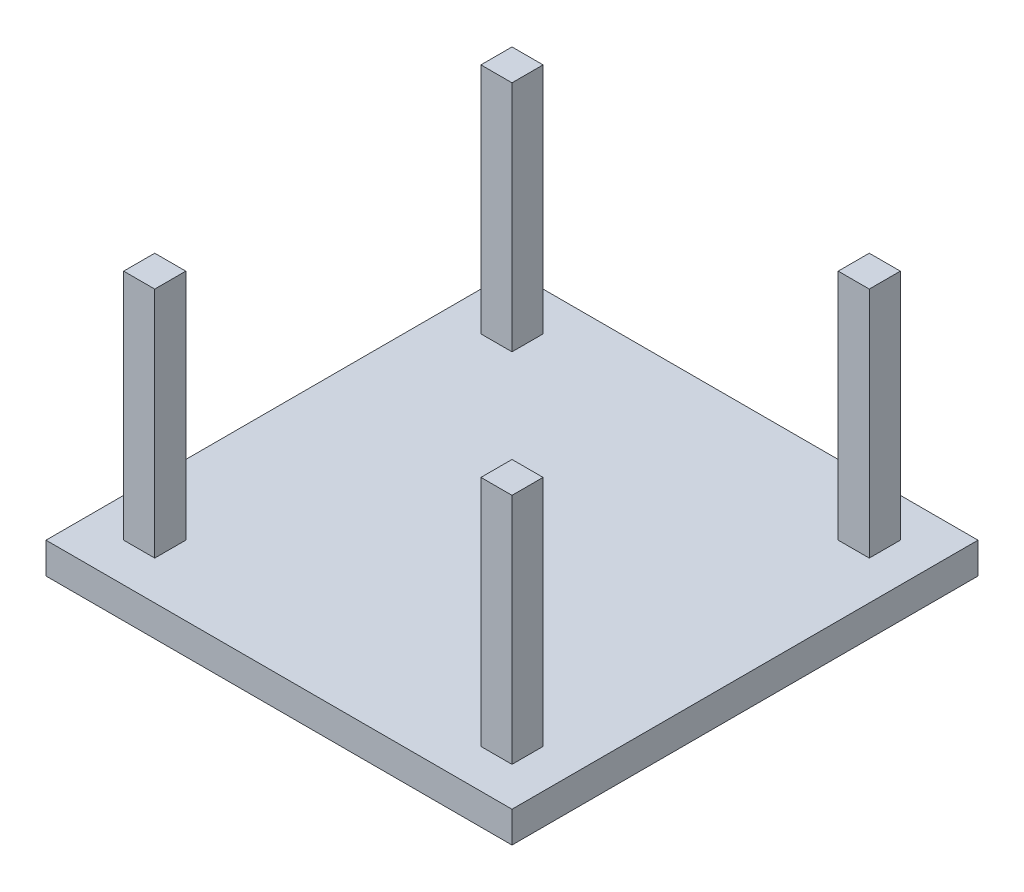
SolidWorks part; units mm, degrees
ref_plane "Front Plane" through (0, 0, 0) normal (0, 0, 1) x (1, 0, 0)
ref_plane "Top Plane" through (0, 0, 0) normal (0, 1, 0) x (1, 0, 0)
ref_plane "Right Plane" through (0, 0, 0) normal (1, 0, 0) x (0, 0, -1)
sketch "Sketch1" plane through (0, 0, 0) normal (0, 1, 0) x (1, 0, 0)
  line L1 (-30, 30) -> (0, 30)
  line L2 (-30, 30) -> (-30, 0)
  line L3 (-30, 0) -> (0, 0)
  line L4 (0, 30) -> (0, 0)
  dimension "D1" = 30
  dimension "D2" = 30
extrude "Boss-Extrude1" add sketch "Sketch1" along normal blind 2
sketch "Sketch2" plane through (0, 2, 0) normal (0, 1, 0) x (1, 0, 0)
  line L0 (-3.5, 4.5) -> (-3.5, 25.5) construction
  line L1 (-27.5, 27.5) -> (-25.5, 27.5)
  line L2 (-27.5, 27.5) -> (-27.5, 25.5)
  line L3 (-27.5, 25.5) -> (-25.5, 25.5)
  line L4 (-25.5, 27.5) -> (-25.5, 25.5)
  line L5 (-4.5, 27.5) -> (-2.5, 27.5)
  line L6 (-4.5, 27.5) -> (-4.5, 25.5)
  line L7 (-4.5, 25.5) -> (-2.5, 25.5)
  line L8 (-2.5, 27.5) -> (-2.5, 25.5)
  line L9 (-4.5, 4.5) -> (-2.5, 4.5)
  line L10 (-4.5, 4.5) -> (-4.5, 2.5)
  line L11 (-4.5, 2.5) -> (-2.5, 2.5)
  line L12 (-2.5, 4.5) -> (-2.5, 2.5)
  line L13 (-27.5, 4.5) -> (-25.5, 4.5)
  line L14 (-27.5, 4.5) -> (-27.5, 2.5)
  line L15 (-27.5, 2.5) -> (-25.5, 2.5)
  line L16 (-25.5, 4.5) -> (-25.5, 2.5)
  line L17 (0, 0) -> (0, 30) construction
  line L18 (-4.5, 26.5) -> (-25.5, 26.5) construction
  line L19 (0, 30) -> (-30, 30) construction
  point P20 (0, 15)
  point P23 (-3.5, 15)
  point P27 (-15, 30)
  point P28 (-15, 26.5)
  dimension "D1" = 2
  dimension "D2" = 2
  dimension "D3" = 2
  dimension "D4" = 2
  dimension "D5" = 2
  dimension "D6" = 2
  dimension "D7" = 21
  dimension "D8" = 21
  dimension "D9" = 2
  dimension "D10" = 2
  dimension "D11" = 21
  dimension "D12" = 21
extrude "Boss-Extrude2" add sketch "Sketch2" along normal blind 15
